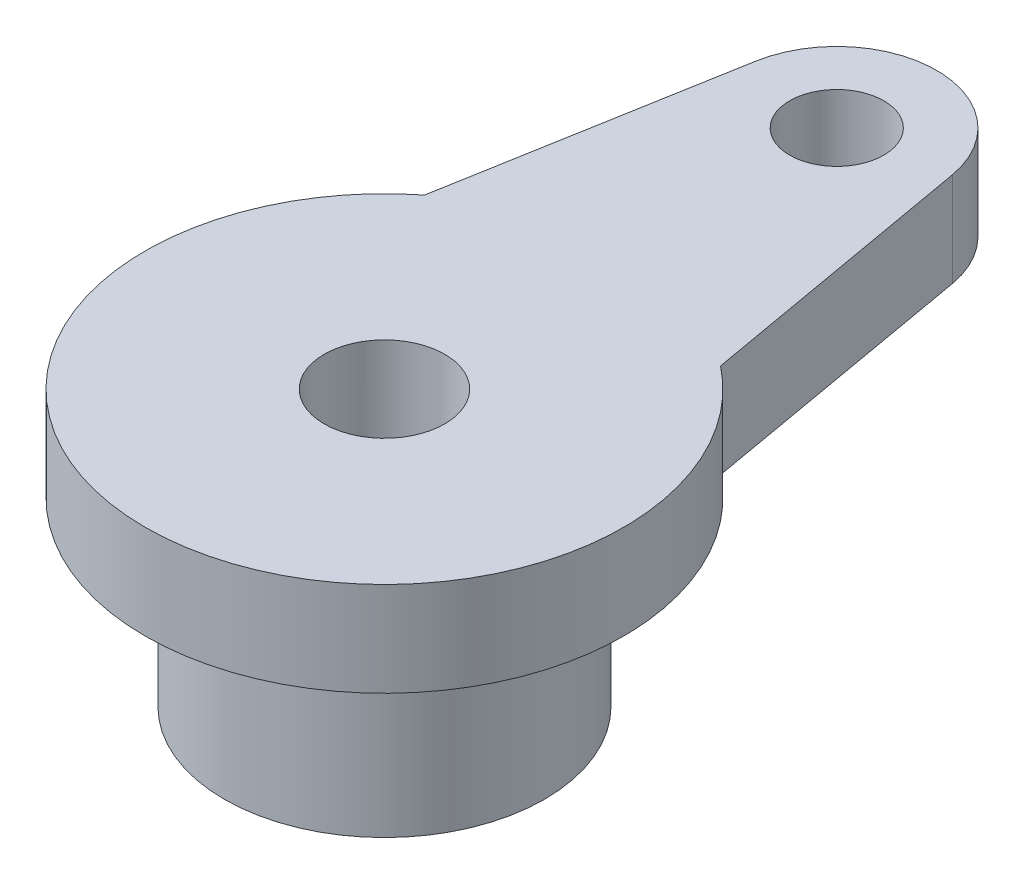
SolidWorks part; units mm, degrees
material "PC High Viscosity"
ref_plane "Front Plane" through (0, 0, 0) normal (0, 0, 1) x (1, 0, 0)
ref_plane "Top Plane" through (0, 0, 0) normal (0, 1, 0) x (1, 0, 0)
ref_plane "Right Plane" through (0, 0, 0) normal (1, 0, 0) x (0, 0, -1)
sketch "BaseS" plane through (0, 0, 0) normal (0, 1, 0) x (1, 0, 0)
  circle A0 centre (0, 0) radius 6.35
  dimension "D1" = 12.7
extrude "BASE" add sketch "BaseS" along normal blind 7.3
sketch "HornHalfS" plane through (0, 7.3, 0) normal (0, 1, 0) x (1, 0, 0)
  line L0 (0, 0) -> (0, 12) construction
  line L1 (-2.6097, 12.4602) -> (-3.9269, 4.9902)
  line L2 (0, 14.65) -> (0, 12) construction
  line L3 (2.6097, 12.4602) -> (3.9269, 4.9902)
  arc A0 (2.6097, 12.4602) -> (-2.6097, 12.4602) centre (0, 12) ccw
  arc A1 (3.9269, 4.9902) -> (-3.9269, 4.9902) centre (0, 0) ccw
  circle A2 centre (0, 0) radius 6.35 construction
  dimension "D1" = 5.3
  dimension "D2" = 14.65
  dimension "D3" = 10
  dimension "D4" = 7.8538
extrude "HORN HALF" add sketch "HornHalfS" against normal blind 2.5
sketch "HornAttachS" plane through (0, 7.3, 0) normal (0, 1, 0) x (1, 0, 0)
  circle A0 centre (0, 12) radius 1.25
  dimension "D1" = 2.5
sketch "ToothS" plane through (0, 0, 0) normal (0, -1, 0) x (1, 0, 0)
  line L0 (0, -3) -> (0.2625, -2.6872)
  line L1 (0, -3) -> (-0.2625, -2.6872)
  line L2 (0, -2.7) -> (0, -3) construction
  line L3 (0, 0) -> (0, -2.7) construction
  arc A0 (-0.2625, -2.6872) -> (0.2625, -2.6872) centre (0, 0) ccw
  dimension "D1" = 5.4
  dimension "D2" = 80
  dimension "D3" = 0.3
extrude "TOOTH" cut sketch "ToothS" against normal blind 3
pattern_circular "TOOTH CP" count 26 over 360 about axis through (0, 0, 0) along (0, 1, 0) of "TOOTH"
sketch "BottomBoreS" plane through (0, 0, 0) normal (0, -1, 0) x (-1, 0, 0)
  circle A0 centre (0, 0) radius 2.7
  arc A1 (0.2625, 2.6872) -> (-0.2625, 2.6872) centre (0, 0) ccw construction
extrude "BOTTOM BORE" cut sketch "BottomBoreS" against normal up to surface (3 mm away)
sketch "HoldingShaftS" plane through (0, 0, 0) normal (0, -1, 0) x (1, 0, 0)
  circle A0 centre (0, 0) radius 6.35 construction
  circle A1 centre (0, 0) radius 6.35
  circle A2 centre (0, 0) radius 4.25
  dimension "D1" = 2.1
  dimension "D2" = 8.5
extrude "HOLDING SHAFT" cut sketch "HoldingShaftS" against normal up to surface (4.8 mm away) up to face at (0, 4.8, -9.6126)
extrude "除料-伸長1" cut sketch "HornAttachS" against normal through all
sketch "TopBoreS" plane through (0, 7.3, 0) normal (0, 1, 0) x (1, 0, 0)
  circle A0 centre (0, 0) radius 1.6
  dimension "D1" = 3.2
extrude "除料-伸長2" cut sketch "TopBoreS" against normal through all
